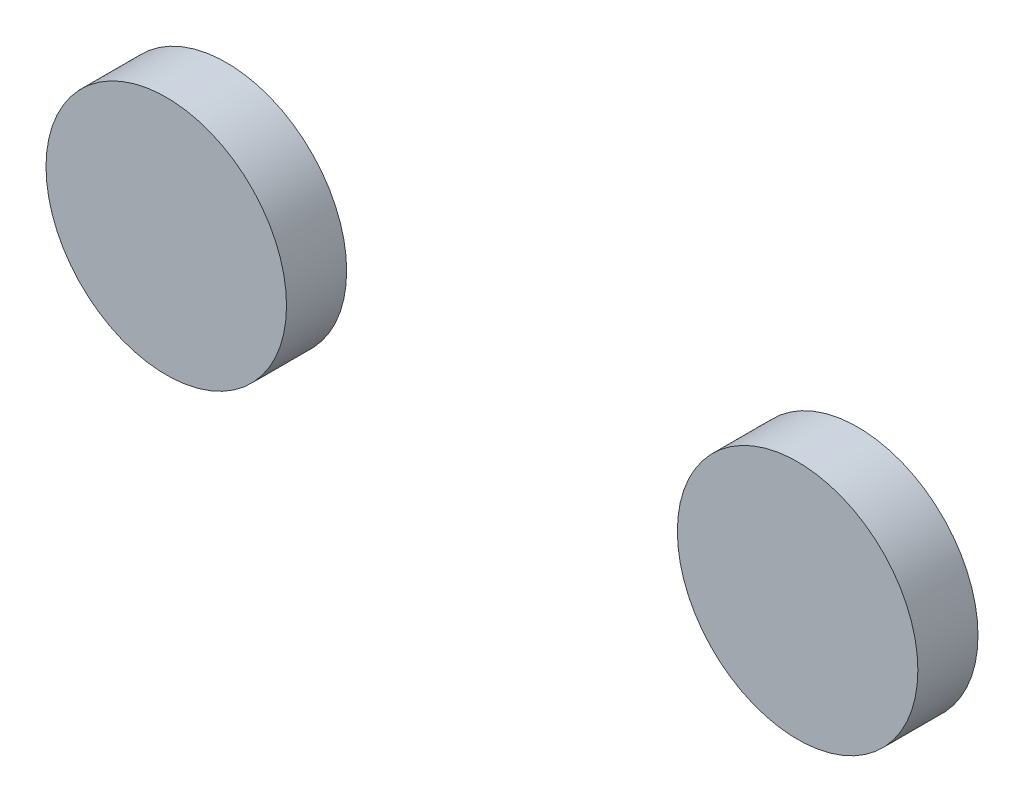
SolidWorks part; units mm, degrees
ref_plane "Front Plane" through (0, 0, 0) normal (0, 0, 1) x (1, 0, 0)
ref_plane "Top Plane" through (0, 0, 0) normal (0, 1, 0) x (1, 0, 0)
ref_plane "Right Plane" through (0, 0, 0) normal (1, 0, 0) x (0, 0, -1)
sketch "Sketch1" plane through (0, 0, 0) normal (0, 0, 1) x (1, 0, 0)
  line L0 (-101.369, 69.9691) -> (98.631, -80.0309)
  line L1 (-101.369, 69.9691) -> (98.631, 69.9691)
  line L2 (-101.369, 69.9691) -> (-101.369, -80.0309)
  line L3 (-101.369, -80.0309) -> (98.631, -80.0309)
  line L4 (98.631, 69.9691) -> (98.631, -80.0309)
  line L5 (-101.369, -80.0309) -> (98.631, 69.9691)
  line L6 (-101.369, -5.0309) -> (98.631, -5.0309)
  circle A3 centre (-51.369, -5.0309) radius 40
  circle A4 centre (53.631, -5.0309) radius 40
  circle A5 centre (-51.369, -5.0309) radius 20
  circle A6 centre (53.631, -5.0309) radius 20
  dimension "D3" = 105
  dimension "D1" = 200
  dimension "D2" = 150
extrude "Boss-Extrude1" add sketch "Sketch1" along normal blind 10 contours L6 A5 | L6 A5 | L6 A6 | L6 A6
